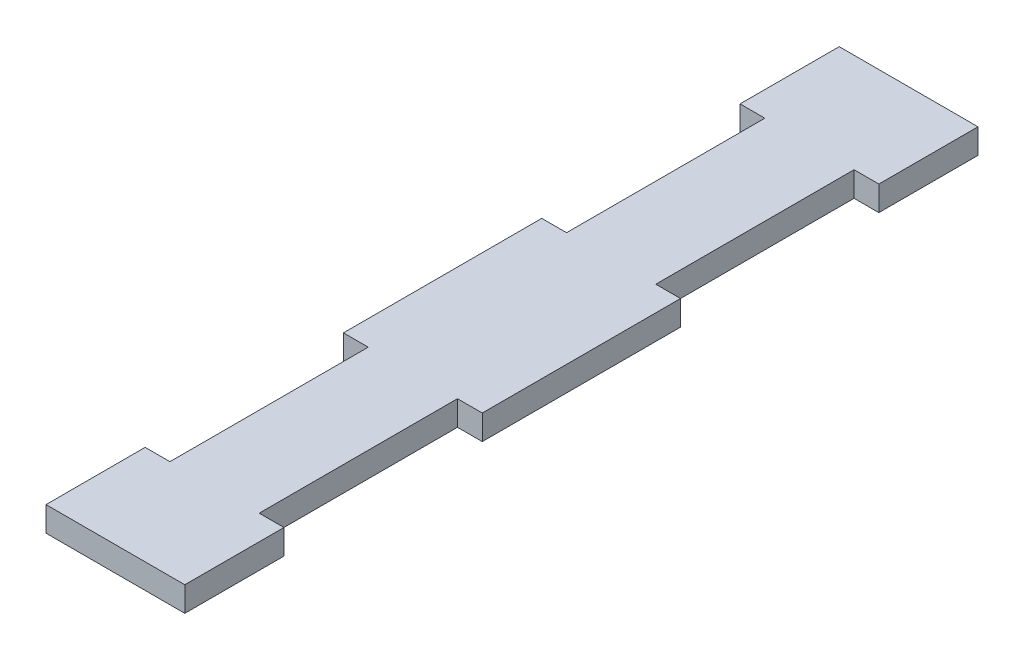
SolidWorks part; units mm, degrees
ref_plane "Front Plane" through (0, 0, 0) normal (0, 0, 1) x (1, 0, 0)
ref_plane "Top Plane" through (0, 0, 0) normal (0, 1, 0) x (1, 0, 0)
ref_plane "Right Plane" through (0, 0, 0) normal (1, 0, 0) x (0, 0, -1)
sketch "Sketch1" plane through (0, 0, 0) normal (0, 1, 0) x (1, 0, 0)
  line L0 (0, 88.9) -> (0, 101.6)
  line L1 (0, 0) -> (17.78, 0)
  line L2 (0, 0) -> (0, 12.7)
  line L3 (0, 101.6) -> (17.78, 101.6)
  line L4 (17.78, 0) -> (17.78, 12.7)
  line L5 (17.78, 88.9) -> (14.605, 88.9)
  line L7 (17.78, 63.5) -> (14.605, 63.5)
  line L8 (14.605, 88.9) -> (14.605, 63.5)
  line L9 (17.78, 38.1) -> (14.605, 38.1)
  line L11 (17.78, 12.7) -> (14.605, 12.7)
  line L12 (14.605, 38.1) -> (14.605, 12.7)
  line L13 (0, 88.9) -> (3.175, 88.9)
  line L15 (0, 63.5) -> (3.175, 63.5)
  line L16 (3.175, 88.9) -> (3.175, 63.5)
  line L17 (0, 38.1) -> (3.175, 38.1)
  line L19 (0, 12.7) -> (3.175, 12.7)
  line L20 (3.175, 38.1) -> (3.175, 12.7)
  line L21 (17.78, 88.9) -> (17.78, 101.6)
  line L22 (0, 38.1) -> (0, 63.5)
  line L23 (17.78, 38.1) -> (17.78, 63.5)
  dimension "D1" = 17.78
  dimension "D2" = 101.6
  dimension "D3" = 12.7
  dimension "D4" = 25.4
  dimension "D5" = 12.7
  dimension "D6" = 25.4
  dimension "D7" = 25.4
  dimension "D8" = 25.4
  dimension "D9" = 12.7
  dimension "D10" = 12.7
  dimension "D11" = 3.175
  dimension "D12" = 3.175
  dimension "D13" = 3.175
  dimension "D14" = 3.175
extrude "Boss-Extrude1" add sketch "Sketch1" along normal blind 3.175
